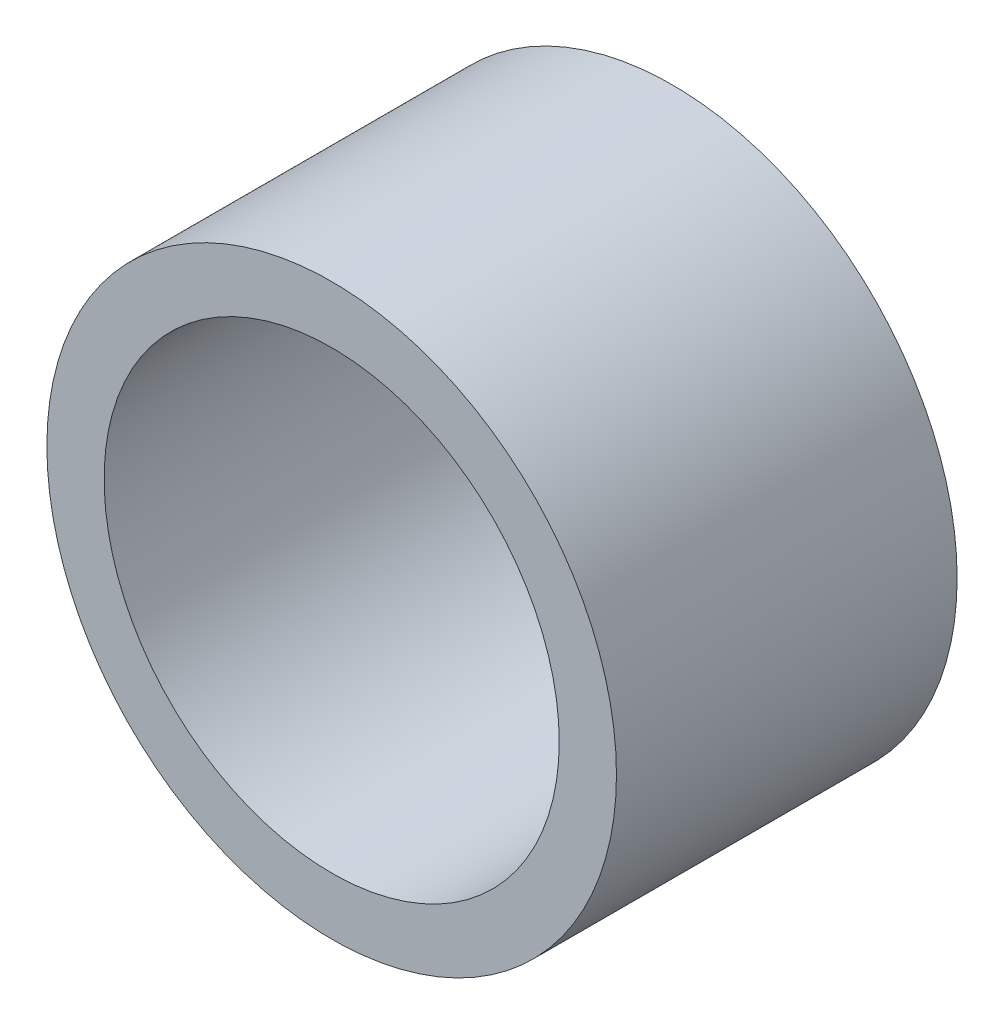
SolidWorks part; units mm, degrees
ref_plane "Front Plane" through (0, 0, 0) normal (0, 0, 1) x (1, 0, 0)
ref_plane "Top Plane" through (0, 0, 0) normal (0, 1, 0) x (1, 0, 0)
ref_plane "Right Plane" through (0, 0, 0) normal (1, 0, 0) x (0, 0, -1)
sketch "Sketch1" plane through (0, 0, 0) normal (0, 0, 1) x (1, 0, 0)
  circle A0 centre (0, 0) radius 7.9629
  circle A1 centre (0, 0) radius 6.3627
  dimension "D1" = 15.9258
  dimension "ID" = 12.7254
extrude "Extrude1" add sketch "Sketch1" along normal mid plane 9.525
sketch "Sketch2" plane through (0, 0, 0) normal (1, 0, 0) x (0, 0, -1)
  line L0 (-4.7625, -6.3627) -> (4.7625, -6.3627) construction
  line L3 (4.7625, 6.3627) -> (-4.7625, 6.3627) construction
  line L5 (-4.7625, -6.3627) -> (4.7625, -6.3627)
  line L6 (4.7625, 6.3627) -> (-4.7625, 6.3627)
sketch "Sketch4" plane through (0, 0, 4.7625) normal (0, 0, 1) x (1, 0, 0)
  line L0 (0, 0) -> (-4.4991, 4.4991)
  line L1 (0, -8.7452) -> (0, 8.7452) construction
  circle A0 centre (0, 0) radius 6.3627 construction
  dimension "D1" = 45
